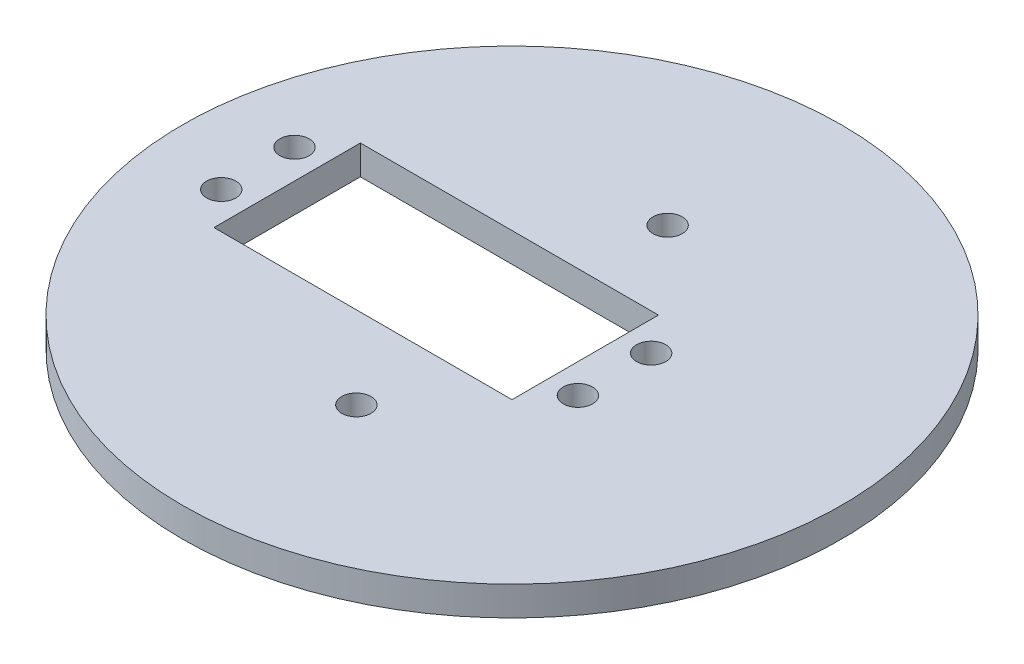
SolidWorks part; units mm, degrees
material "Acrílico (Impacto medio-alto)"
ref_plane "Piano frontale" through (0, 0, 0) normal (0, 0, 1) x (1, 0, 0)
ref_plane "Piano superiore" through (0, 0, 0) normal (0, 1, 0) x (1, 0, 0)
ref_plane "Piano destro" through (0, 0, 0) normal (1, 0, 0) x (0, 0, -1)
sketch "Schizzo1" plane through (0, 0, 0) normal (0, 1, 0) x (1, 0, 0)
  line L0 (-42.1632, 0) -> (43.9871, 0) construction
  line L1 (0, 27.25) -> (0, 0) construction
  line L2 (-25, 37.4166) -> (-25, 27.25) construction
  line L3 (-25, 27.25) -> (25, 27.25) construction
  line L4 (25, 37.4166) -> (25, 27.25) construction
  line L5 (0, 0) -> (0, -27.25) construction
  line L8 (-25, -37.4166) -> (-25, -27.25) construction
  line L9 (-25, -27.25) -> (25, -27.25) construction
  line L10 (25, -37.4166) -> (25, -27.25) construction
  arc A0 (-25, 37.4166) -> (-25, -37.4166) centre (0, 0) ccw construction
  arc A1 (25, -37.4166) -> (25, 37.4166) centre (0, 0) ccw construction
  circle A2 centre (0, 0) radius 45
  point P3 (0, 45)
  point P8 (0, -45)
  dimension "D1" = 90
  dimension "D2" = 54.5
  dimension "D3" = 25
  dimension "D4" = 25
extrude "Estrusione-Estrusione1" add sketch "Schizzo1" along normal mid plane 4
sketch "Croquis1" plane through (0, 2, 0) normal (0, 1, 0) x (1, 0, 0)
  line L1 (-30.7, 10) -> (10, 10)
  line L2 (-30.7, 10) -> (-30.7, -10)
  line L3 (-30.7, -10) -> (10, -10)
  line L4 (10, 10) -> (10, -10)
  circle A0 centre (-34.7, 5) radius 2 construction
  circle A1 centre (-34.7, -5) radius 2 construction
  circle A2 centre (0, -21.25) radius 2 construction
  circle A3 centre (0, 21.25) radius 2 construction
  circle A4 centre (14, 5) radius 2 construction
  circle A5 centre (14, -5) radius 2 construction
  circle A6 centre (-34.7, 5) radius 2
  circle A7 centre (-34.7, -5) radius 2
  circle A8 centre (0, -21.25) radius 2
  circle A9 centre (0, 21.25) radius 2
  circle A10 centre (14, 5) radius 2
  circle A11 centre (14, -5) radius 2
extrude "Cortar-Extruir1" cut sketch "Croquis1" against normal blind 10
